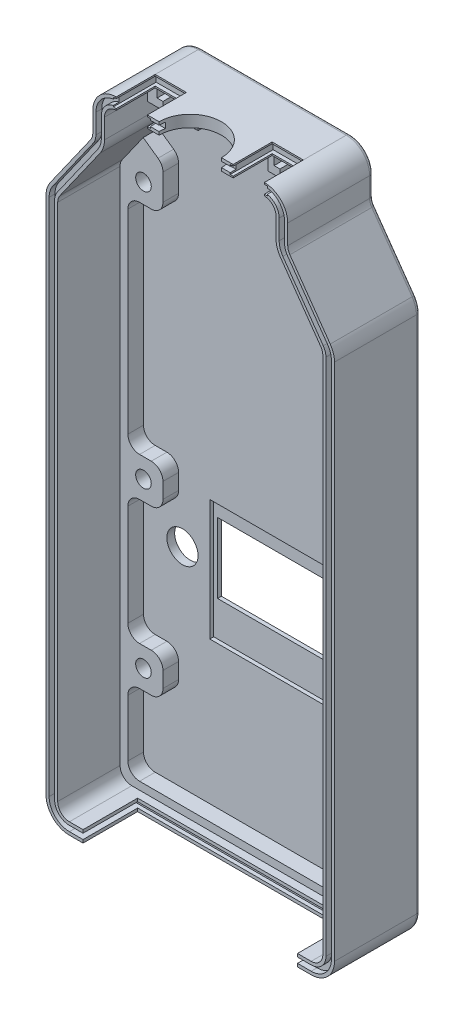
SolidWorks part; units mm, degrees
ref_plane "Front Plane" through (0, 0, 0) normal (0, 0, 1) x (1, 0, 0)
ref_plane "Top Plane" through (0, 0, 0) normal (0, 1, 0) x (1, 0, 0)
ref_plane "Right Plane" through (0, 0, 0) normal (1, 0, 0) x (0, 0, -1)
sketch "Sketch3" plane through (0, 0, 0) normal (0, 0, 1) x (1, 0, 0)
  line L1 (-37, -85) -> (37, -85)
  line L2 (-37, -85) -> (-37, 85)
  line L3 (-37, 85) -> (37, 85)
  line L4 (37, -85) -> (37, 85)
  line L5 (-37, -85) -> (37, 85) construction
  line L6 (-37, 85) -> (37, -85) construction
  point P0 (0, 0)
  dimension "D1" = 170
  dimension "D2" = 74
extrude "Boss-Extrude1" add sketch "Sketch3" along normal blind 2
sketch "Sketch4" plane through (0, 0, 2) normal (0, 0, 1) x (1, 0, 0)
  line L0 (-25, 73) -> (-37, 56)
  line L1 (37, 85) -> (-37, 85) construction
  line L2 (37, -85) -> (37, 85) construction
  line L3 (-37, 56) -> (-37, 85)
  line L6 (25, 73) -> (37, 56)
  line L7 (-37, 85) -> (-37, -85) construction
  line L8 (37, 56) -> (37, 85)
  line L9 (-25, 73) -> (-25, 85)
  line L10 (-25, 85) -> (-37, 85)
  line L11 (37, 85) -> (25, 85)
  line L12 (25, 85) -> (25, 73)
  dimension "D1" = 12
  dimension "D2" = 29
  dimension "D3" = 12
  dimension "D4" = 29
  dimension "D5" = 12
  dimension "D6" = 12
extrude "Cut-Extrude1" cut sketch "Sketch4" against normal up to surface (2 mm away) up to face at (0, 0, 0)
sketch "Sketch5" plane through (0, 0, 2) normal (0, 0, 1) x (1, 0, 0)
  line L1 (-25, 85) -> (25, 85)
  line L3 (37, 56) -> (37, -85)
  line L4 (37, -85) -> (-37, -85)
  line L5 (-37, -85) -> (-37, 56)
  line L7 (-22, 82) -> (22, 82)
  line L9 (34, 55.0478) -> (34, -82)
  line L10 (34, -82) -> (-34, -82)
  line L11 (-34, -82) -> (-34, 55.0478)
  line L12 (-22, 82) -> (-22, 72.0478)
  line L13 (-22, 72.0478) -> (-34, 55.0478)
  line L14 (-25, 85) -> (-25, 73)
  line L15 (-25, 73) -> (-37, 56)
  line L16 (25, 85) -> (25, 73)
  line L17 (25, 73) -> (37, 56)
  line L18 (34, 55.0478) -> (22, 72.0478)
  line L19 (22, 72.0478) -> (22, 82)
  line L21 (25, 85) -> (-25, 85) construction
  line L22 (-25, 73) -> (-25, 85) construction
  line L23 (-37, 56) -> (-25, 73) construction
  line L24 (-37, 56) -> (-37, -85) construction
  line L25 (-37, -85) -> (37, -85) construction
  line L26 (37, -85) -> (37, 56) construction
  line L27 (25, 85) -> (25, 73) construction
  line L28 (25, 73) -> (37, 56) construction
  dimension "D1" = 3
  dimension "D2" = 3
  dimension "D3" = 3
  dimension "D4" = 3
  dimension "D5" = 3
  dimension "D6" = 3
  dimension "D7" = 3
  dimension "D8" = 3
extrude "Boss-Extrude2" add sketch "Sketch5" along normal blind 20
sketch "Sketch6" plane through (0, 0, 2) normal (0, 0, 1) x (1, 0, 0)
  line L0 (34, -82) -> (34, 55.0478) construction
  line L1 (34, 55.0478) -> (22, 72.0478) construction
  line L2 (-34, -82) -> (34, -82) construction
  line L6 (34, -82) -> (34, 55.0478)
  line L12 (-23, 59.8565) -> (-23, 48.5936)
  line L13 (-23, 48.5936) -> (-32, 48.5936)
  line L14 (-32, 48.5936) -> (-32, -7.4064)
  line L15 (-32, -7.4064) -> (-23, -7.4064)
  line L16 (-23, -7.4064) -> (-23, -17.4064)
  line L17 (-23, -17.4064) -> (-32, -17.4064)
  line L18 (-32, -17.4064) -> (-32, -49.4064)
  line L19 (-32, -49.4064) -> (-23, -49.4064)
  line L20 (-23, -49.4064) -> (-23, -59.4064)
  line L21 (-23, -59.4064) -> (-32, -59.4064)
  line L22 (-32, -59.4064) -> (-32, -80)
  line L23 (-32, -80) -> (32, -80)
  line L24 (32, -80) -> (32, -59.4064)
  line L25 (32, -59.4064) -> (23, -59.4064)
  line L26 (23, -59.4064) -> (23, -49.4064)
  line L27 (23, -49.4064) -> (32, -49.4064)
  line L28 (32, -49.4064) -> (32, -17.4064)
  line L29 (32, -17.4064) -> (23, -17.4064)
  line L30 (23, -17.4064) -> (23, -7.4064)
  line L31 (23, -7.4064) -> (32, -7.4064)
  line L32 (32, -7.4064) -> (32, 48.5936)
  line L33 (32, 48.5936) -> (23, 48.5936)
  line L34 (23, 48.5936) -> (23, 59.8565)
  line L39 (28.0763, 63.4398) -> (34, 55.0478)
  line L41 (-28.0763, 63.4398) -> (-34, 55.0478)
  line L42 (-34, 55.0478) -> (-34, -82)
  line L43 (-34, -82) -> (34, -82)
  line L44 (-34, 55.0478) -> (-34, -82) construction
  line L45 (-22, 72.0478) -> (-34, 55.0478) construction
  line L49 (-23, 59.8565) -> (-28.0763, 63.4398)
  line L50 (23, 59.8565) -> (28.0763, 63.4398)
  circle A0 centre (28, -54.4064) radius 2
  circle A1 centre (-28, -54.4064) radius 2
  circle A2 centre (28, -12.4064) radius 2
  circle A3 centre (-28, -12.4064) radius 2
  circle A4 centre (-28, 53.5936) radius 2
  circle A5 centre (28, 53.5936) radius 2
  dimension "D1" = 4
  dimension "D2" = 4
  dimension "D5" = 6
  dimension "D6" = 6
  dimension "D7" = 4
  dimension "D8" = 4
  dimension "D9" = 42
  dimension "D10" = 42
  dimension "D11" = 56
  dimension "D12" = 0
  dimension "D13" = 0
  dimension "D14" = 4
  dimension "D15" = 4
  dimension "D16" = 66
  dimension "D17" = 66
  dimension "D18" = 0
  dimension "D19" = 0
  dimension "D30" = 5
  dimension "D31" = 5
  dimension "D34" = 5
  dimension "D36" = 5
  dimension "D37" = 5
  dimension "D38" = 5
  dimension "D40" = 5
  dimension "D39" = 5
  dimension "D41" = 5
  dimension "D43" = 5
  dimension "D46" = 5
  dimension "D25" = 8
  dimension "D28" = 8
  dimension "D20" = 2
  dimension "D21" = 2
  dimension "D22" = 2
  dimension "D23" = 2
  dimension "D24" = 2
  dimension "D26" = 2
  dimension "D27" = 2
  dimension "D32" = 5
  dimension "D33" = 5
  dimension "D35" = 5
  dimension "D42" = 5
  dimension "D45" = 5
extrude "Boss-Extrude3" add sketch "Sketch6" along normal blind 4
fillet "Fillet1" radius 3 24 edges at (-23, 48.5936, 4) (-23, 59.8565, 4) (23, 59.8565, 4) (23, 48.5936, 4) (32, 48.5936, 4) (32, -7.4064, 4) (23, -7.4064, 4) (23, -17.4064, 4) (32, -17.4064, 4) (32, -49.4064, 4) (23, -49.4064, 4) (23, -59.4064, 4) (32, -59.4064, 4) (32, -80, 4) (-32, -80, 4) (-32, -59.4064, 4) (-23, -59.4064, 4) (-23, -49.4064, 4) (-32, -49.4064, 4) (-32, -17.4064, 4) (-23, -17.4064, 4) (-23, -7.4064, 4) (-32, -7.4064, 4) (-32, 48.5936, 4)
fillet "Fillet2" radius 6 8 edges at (-25, 85, 11) (37, -85, 11) (-37, -85, 11) (22, 72.0478, 12) (-22, 72.0478, 12) (-37, 56, 11) (37, 56, 11) (25, 85, 11)
fillet "Fillet3" radius 3 8 edges at (-22, 82, 12) (34, -82, 14) (-34, -82, 14) (34, 55.0478, 14) (-34, 55.0478, 14) (25, 73, 11) (-25, 73, 11) (22, 82, 12)
fillet "Fillet4" radius 1 16 edges at (36.7189, 55.9108, 0) (30.7255, 64.8889, 0) (25.1406, 73.0446, 0) (25, 76.4761, 0) (23.2426, 83.2426, 0) (0, 85, 0) (-23.2426, 83.2426, 0) (-25, 76.4761, 0) (-25.1406, 73.0446, 0) (-30.7255, 64.8889, 0) (-36.7189, 55.9108, 0) (-37, -12.4522, 0) (-35.2426, -83.2426, 0) (0, -85, 0) (35.2426, -83.2426, 0) (37, -12.4522, 0)
sketch "Sketch7" plane through (0, 0, 2) normal (0, 0, 1) x (1, 0, 0)
  circle A0 centre (-22, -26.4064) radius 4
  circle A1 centre (22, -26.4064) radius 4
  circle A5 centre (28, -12.4064) radius 2 construction
  circle A6 centre (-28, -12.4064) radius 2 construction
  circle A7 centre (-28, -12.4064) radius 2 construction
  dimension "D1" = 8
  dimension "D2" = 8
  dimension "D3" = 14
  dimension "D4" = 6
  dimension "D5" = 6
  dimension "D6" = 14
extrude "Cut-Extrude2" cut sketch "Sketch7" against normal up to surface (2 mm away) up to face at (0, 32.0858, 0)
sketch "Sketch8" plane through (0, 0, 2) normal (0, 0, 1) x (1, 0, 0)
  line L1 (-14, -16.4064) -> (14, -16.4064)
  line L2 (-14, -16.4064) -> (-14, -34.4064)
  line L3 (-14, -34.4064) -> (14, -34.4064)
  line L4 (14, -16.4064) -> (14, -34.4064)
  circle A0 centre (28, -12.4064) radius 2 construction
  circle A1 centre (28, -12.4064) radius 2 construction
  circle A2 centre (-28, -12.4064) radius 2 construction
  dimension "D1" = 4
  dimension "D2" = 14
  dimension "D4" = 18
  dimension "D3" = 14
extrude "Cut-Extrude8" cut sketch "Sketch8" against normal up to surface (2 mm away) up to face at (-26, -26.4064, 0)
sketch "Sketch9" plane through (0, 0, 2) normal (0, 0, 1) x (1, 0, 0)
  line L1 (-15, -12.4064) -> (15, -12.4064)
  line L2 (-15, -12.4064) -> (-15, -43.4064)
  line L3 (-15, -43.4064) -> (15, -43.4064)
  line L4 (15, -12.4064) -> (15, -43.4064)
  line L7 (-14, -34.4064) -> (14, -34.4064) construction
  line L8 (14, -34.4064) -> (14, -16.4064) construction
  line L9 (-14, -16.4064) -> (-14, -34.4064) construction
  dimension "D1" = 31
  dimension "D2" = 9
  dimension "D3" = 1
  dimension "D4" = 1
extrude "Cut-Extrude9" cut sketch "Sketch9" against normal blind 1
sketch "Sketch14" plane through (0, 0, 22) normal (0, 0, 1) x (1, 0, 0)
  line L0 (-19, 84.2) -> (19, 84.2)
  line L1 (-19, 82.8) -> (19, 82.8)
  line L2 (19, 85) -> (-19, 85) construction
  line L3 (19, 82) -> (-19, 82) construction
  line L4 (-24.2, 79) -> (-24.2, 73.9522)
  line L5 (-22.8, 79) -> (-22.8, 73.9522)
  line L6 (-22, 79) -> (-22, 73.9522) construction
  line L7 (-25, 79) -> (-25, 73.9522) construction
  line L8 (-24.8955, 71.7608) -> (-35.2482, 57.0944)
  line L9 (-23.7518, 70.9534) -> (-34.1045, 56.2871)
  line L10 (-25.5491, 72.2221) -> (-35.9018, 57.5558) construction
  line L11 (-23.0982, 70.4921) -> (-28.0763, 63.4398) construction
  line L12 (-34.8, 54.0957) -> (-34.8, -79)
  line L13 (-36.2, 54.0957) -> (-36.2, -79)
  line L14 (-34, 54.0957) -> (-34, -79) construction
  line L15 (-37, 54.0957) -> (-37, -79) construction
  line L16 (-31, -82.8) -> (31, -82.8)
  line L17 (-31, -84.2) -> (31, -84.2)
  line L18 (-31, -82) -> (31, -82) construction
  line L19 (-31, -85) -> (31, -85) construction
  line L20 (22.8, 79) -> (22.8, 73.9522)
  line L21 (24.2, 79) -> (24.2, 73.9522)
  line L22 (22, 73.9522) -> (22, 79) construction
  line L23 (25, 73.9522) -> (25, 79) construction
  line L24 (24.8955, 71.7608) -> (35.2482, 57.0944)
  line L25 (23.7518, 70.9534) -> (34.1045, 56.2871)
  line L26 (35.9018, 57.5558) -> (25.5491, 72.2221) construction
  line L27 (28.0763, 63.4398) -> (23.0982, 70.4921) construction
  line L28 (36.2, 54.0957) -> (36.2, -79)
  line L29 (34.8, 54.0957) -> (34.8, -79)
  line L30 (37, -79) -> (37, 54.0957) construction
  line L31 (34, -79) -> (34, 54.0957) construction
  arc A0 (-19, 84.2) -> (-24.2, 79) centre (-19, 79) ccw
  arc A1 (-19, 82.8) -> (-22.8, 79) centre (-19, 79) ccw
  arc A2 (-19, 82) -> (-22, 79) centre (-19, 79) ccw construction
  arc A3 (-24.2, 73.9522) -> (-24.8955, 71.7608) centre (-28, 73.9522) cw
  arc A4 (-22.8, 73.9522) -> (-23.7518, 70.9534) centre (-28, 73.9522) cw
  arc A5 (-25.5491, 72.2221) -> (-25, 73.9522) centre (-28, 73.9522) ccw construction
  arc A6 (-35.2482, 57.0944) -> (-36.2, 54.0957) centre (-31, 54.0957) ccw
  arc A7 (-34.1045, 56.2871) -> (-34.8, 54.0957) centre (-31, 54.0957) ccw
  arc A8 (-33.4509, 55.8257) -> (-34, 54.0957) centre (-31, 54.0957) ccw construction
  arc A9 (-34.8, -79) -> (-31, -82.8) centre (-31, -79) ccw
  arc A10 (-36.2, -79) -> (-31, -84.2) centre (-31, -79) ccw
  arc A11 (-34, -79) -> (-31, -82) centre (-31, -79) ccw construction
  arc A12 (19, 82.8) -> (22.8, 79) centre (19, 79) cw
  arc A13 (19, 84.2) -> (24.2, 79) centre (19, 79) cw
  arc A14 (22, 79) -> (19, 82) centre (19, 79) ccw construction
  arc A15 (24.2, 73.9522) -> (24.8955, 71.7608) centre (28, 73.9522) ccw
  arc A16 (22.8, 73.9522) -> (23.7518, 70.9534) centre (28, 73.9522) ccw
  arc A17 (25, 73.9522) -> (25.5491, 72.2221) centre (28, 73.9522) ccw construction
  arc A18 (34.1045, 56.2871) -> (34.8, 54.0957) centre (31, 54.0957) cw
  arc A19 (35.2482, 57.0944) -> (36.2, 54.0957) centre (31, 54.0957) cw
  arc A20 (34, 54.0957) -> (33.4509, 55.8257) centre (31, 54.0957) ccw construction
  arc A21 (34.8, -79) -> (31, -82.8) centre (31, -79) cw
  arc A22 (36.2, -79) -> (31, -84.2) centre (31, -79) cw
  arc A23 (31, -82) -> (34, -79) centre (31, -79) ccw construction
  dimension "D3" = 0.8
  dimension "D5" = 0.8
  dimension "D7" = 0.8
  dimension "D9" = 0.8
  dimension "D11" = 0.8
  dimension "D13" = 0.8
  dimension "D15" = 0.8
  dimension "D1" = 0.8
  dimension "D2" = 0.8
  dimension "D4" = 0.8
  dimension "D6" = 0.8
  dimension "D8" = 0.8
  dimension "D10" = 0.8
  dimension "D12" = 0.8
  dimension "D14" = 0.8
  dimension "D16" = 0.8
extrude "Cut-Extrude13" cut sketch "Sketch14" against normal blind 1.5
sketch "Sketch10" plane through (0, 82, 0) normal (0, -1, 0) x (1, 0, 0)
  line L1 (19, 2) -> (19, 22) construction
  line L5 (19, 22) -> (-19, 22) construction
  circle A0 centre (0, 22) radius 8
  dimension "D1" = 16
  dimension "D2" = 19
  dimension "D3" = 0
extrude "Cut-Extrude10" cut sketch "Sketch10" against normal up to surface (3 mm away) contours A0 up to face at (0, 85, 11.5)
sketch "Sketch11" plane through (0, 0, 22) normal (0, 0, 1) x (1, 0, 0)
  line L1 (-19, 85) -> (-11, 85)
  line L2 (-19, 85) -> (-19, 82)
  line L3 (-19, 82) -> (-11, 82)
  line L4 (-11, 85) -> (-11, 82)
  line L8 (11, 85) -> (19, 85)
  line L9 (11, 85) -> (11, 82)
  line L10 (11, 82) -> (19, 82)
  line L11 (19, 85) -> (19, 82)
  line L15 (19, 82) -> (8, 82) construction
  line L16 (19, 85) -> (8, 85) construction
  line L17 (-8, 85) -> (-19, 85) construction
  line L18 (-8, 82) -> (-19, 82) construction
  dimension "D1" = 8
  dimension "D3" = 8
extrude "Cut-Extrude11" cut sketch "Sketch11" against normal blind 10
sketch "Sketch16" plane through (0, 0, 2) normal (0, 0, 1) x (1, 0, 0)
  line L0 (-8, 82) -> (-11, 82) construction
  line L1 (-9, 82) -> (-22, 82)
  line L2 (-9, 82) -> (-9, 77)
  line L3 (-9, 77) -> (-22, 77)
  line L4 (-22, 82) -> (-22, 77)
  line L5 (-22, 79) -> (-22, 73.9522) construction
  line L6 (-22, 79) -> (-22, 73.9522) construction
  line L7 (19, 82) -> (-19, 82) construction
  line L8 (-11, 82) -> (-11, 85) construction
  line L9 (22, 73.9522) -> (22, 79) construction
  line L10 (9, 82) -> (22, 82)
  line L11 (9, 82) -> (9, 77)
  line L12 (9, 77) -> (22, 77)
  line L13 (22, 82) -> (22, 77)
  line L14 (11, 85) -> (11, 82) construction
  dimension "D1" = 2
  dimension "D2" = 2
  dimension "D3" = 5
  dimension "D4" = 5
extrude "Boss-Extrude5" add sketch "Sketch16" along normal blind 5
sketch "Sketch12" plane through (0, 0, 7) normal (0, 0, 1) x (1, 0, 0)
  line L0 (-22, 82) -> (-18, 82)
  line L1 (-18, 82) -> (-18, 81)
  line L2 (-18, 81) -> (-19.5, 81)
  line L3 (-19.5, 81) -> (-19.5, 79)
  line L4 (-19.5, 79) -> (-18, 79)
  line L5 (-18, 79) -> (-18, 77)
  line L6 (-18, 77) -> (-22, 77)
  line L7 (-22, 77) -> (-22, 82)
  line L9 (-12, 82) -> (-9, 82)
  line L10 (-9, 82) -> (-9, 77)
  line L11 (-9, 77) -> (-12, 77)
  line L12 (-12, 77) -> (-12, 79)
  line L13 (-12, 79) -> (-10.5, 79)
  line L14 (-10.5, 79) -> (-10.5, 81)
  line L15 (-10.5, 81) -> (-12, 81)
  line L16 (-12, 81) -> (-12, 82)
  line L17 (9, 82) -> (-9, 82) construction
  line L18 (22, 73.9522) -> (22, 77) construction
  line L19 (9, 82) -> (12, 82)
  line L20 (12, 82) -> (12, 81)
  line L21 (12, 81) -> (10.5, 81)
  line L22 (10.5, 81) -> (10.5, 79)
  line L23 (10.5, 79) -> (12, 79)
  line L24 (12, 79) -> (12, 77)
  line L25 (12, 77) -> (9, 77)
  line L26 (9, 77) -> (9, 82)
  line L27 (18, 82) -> (22, 82)
  line L28 (22, 82) -> (22, 77)
  line L29 (22, 77) -> (18, 77)
  line L30 (18, 77) -> (18, 79)
  line L31 (18, 79) -> (19.5, 79)
  line L32 (19.5, 79) -> (19.5, 81)
  line L33 (19.5, 81) -> (18, 81)
  line L34 (18, 81) -> (18, 82)
  line L35 (11, 82) -> (8, 82) construction
  line L36 (-22, 77) -> (-22, 73.9522) construction
  dimension "D1" = 1
  dimension "D2" = 2
  dimension "D3" = 2
  dimension "D4" = 1.5
  dimension "D5" = 1.5
  dimension "D6" = 1
  dimension "D7" = 1
  dimension "D8" = 2
  dimension "D9" = 2
  dimension "D10" = 3
  dimension "D11" = 1.5
  dimension "D12" = 1.5
  dimension "D13" = 1
  dimension "D14" = 1
  dimension "D15" = 1
  dimension "D16" = 2
  dimension "D17" = 2
  dimension "D18" = 1.5
  dimension "D19" = 1.5
  dimension "D20" = 3
  dimension "D21" = 1
  dimension "D22" = 2
  dimension "D23" = 2
  dimension "D24" = 1
  dimension "D25" = 1.5
  dimension "D26" = 1.5
extrude "Boss-Extrude4" add sketch "Sketch12" along normal blind 4
sketch "Sketch13" plane through (0, 0, 22) normal (0, 0, 1) x (1, 0, 0)
  line L1 (-10.25, 84.6) -> (-19.75, 84.6)
  line L2 (-10.25, 84.6) -> (-10.25, 82.4)
  line L3 (-10.25, 82.4) -> (-19.75, 82.4)
  line L4 (-19.75, 84.6) -> (-19.75, 82.4)
  line L6 (19.75, 84.6) -> (10.25, 84.6)
  line L7 (19.75, 84.6) -> (19.75, 82.4)
  line L8 (19.75, 82.4) -> (10.25, 82.4)
  line L9 (10.25, 84.6) -> (10.25, 82.4)
  line L12 (-11, 82) -> (-11, 82.8) construction
  line L13 (-8, 85) -> (-11, 85) construction
  line L15 (11, 85) -> (8, 85) construction
  line L16 (11, 85) -> (11, 84.2) construction
  dimension "D1" = 0.75
  dimension "D2" = 2.2
  dimension "D3" = 9.5
  dimension "D4" = 0.4
  dimension "D5" = 0.4
  dimension "D6" = 2.2
  dimension "D7" = 9.5
  dimension "D8" = 0.75
extrude "Cut-Extrude12" cut sketch "Sketch13" against normal blind 11
sketch "Sketch15" plane through (0, 0, 22) normal (0, 0, 1) x (1, 0, 0)
  line L0 (-27.5, -82) -> (-27.5, -82.8)
  line L1 (-31, -82) -> (31, -82) construction
  line L2 (-31, -82.8) -> (31, -82.8) construction
  line L3 (-27.5, -82.8) -> (-29, -82.8)
  line L4 (-29, -82.8) -> (-29, -84.2)
  line L5 (-31, -84.2) -> (31, -84.2) construction
  line L6 (-29, -84.2) -> (-27.5, -84.2)
  line L7 (-31, -84.2) -> (31, -84.2) construction
  line L8 (-27.5, -84.2) -> (-27.5, -85)
  line L9 (-31, -85) -> (31, -85) construction
  line L10 (-27.5, -85) -> (27.5, -85)
  line L11 (27.5, -85) -> (27.5, -84.2)
  line L12 (27.5, -84.2) -> (29, -84.2)
  line L13 (29, -84.2) -> (29, -82.8)
  line L14 (29, -82.8) -> (27.5, -82.8)
  line L15 (-31, -82.8) -> (31, -82.8) construction
  line L16 (27.5, -82.8) -> (27.5, -82)
  line L17 (27.5, -82) -> (-27.5, -82)
  dimension "D1" = 2
  dimension "D2" = 1.5
  dimension "D3" = 1.5
  dimension "D4" = 1.5
  dimension "D5" = 1.5
  dimension "D6" = 2
extrude "Cut-Extrude14" cut sketch "Sketch15" against normal blind 14
fillet "Fillet5" radius 3 2 edges at (9, 79.5, 2) (-9, 79.5, 2)
sketch "Sketch17" plane through (0, 0, 8) normal (0, 0, 1) x (1, 0, 0)
  line L0 (-29, -82.8) -> (29, -82.8)
  line L1 (29, -82.8) -> (29, -84.2)
  line L2 (29, -84.2) -> (-29, -84.2)
  line L3 (-29, -84.2) -> (-29, -82.8)
extrude "Cut-Extrude15" cut sketch "Sketch17" against normal blind 1
